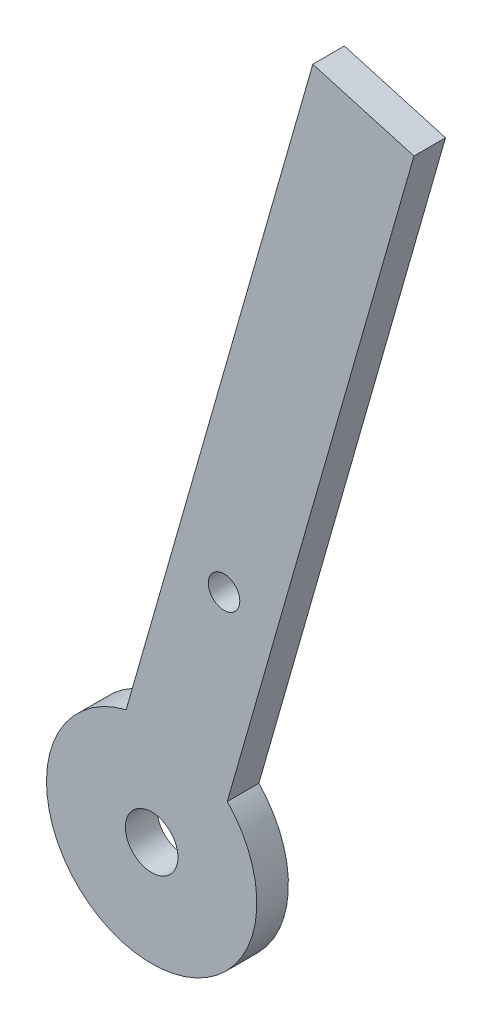
SolidWorks part; units mm, degrees
ref_plane "Front Plane" through (0, 0, 0) normal (0, 0, 1) x (1, 0, 0)
ref_plane "Top Plane" through (0, 0, 0) normal (0, 1, 0) x (1, 0, 0)
ref_plane "Right Plane" through (0, 0, 0) normal (1, 0, 0) x (0, 0, -1)
sketch "Sketch1" plane through (0, 0, 0) normal (0, 0, 1) x (1, 0, 0)
  line L2 (-60, 60) -> (128.1618, 60) construction
  line L4 (-60, -60) -> (111.0248, -60) construction
  line L8 (-60, 60) -> (-60, -60) construction
  line L10 (-87.0843, -3.037) -> (-104.8279, -65.0493)
  line L11 (-87.0843, -3.037) -> (-96.6985, -0.2861)
  line L12 (-96.6985, -0.2861) -> (-114.4421, -62.2984)
  line L13 (-112.0173, -72) -> (-91.8914, -1.6615) construction
  line L15 (-60, -60) -> (-125, -60) construction
  line L16 (-60, 60) -> (-125, 60) construction
  circle A7 centre (0, 0) radius 60 construction
  circle A9 centre (-125, 0) radius 60 construction
  arc A10 (-114.4421, -62.2984) -> (-104.8279, -65.0493) centre (-112.0173, -72) ccw
  circle A11 centre (-112.0173, -72) radius 2.5
  circle A12 centre (-105.1401, -47.9645) radius 1.5
  circle A14 centre (-112.0173, -72) radius 73.1611 construction
  point P16 (-40.3908, -55.5605)
  point P17 (-159.7602, -14.5505)
  point P18 (-158.6202, -13.8776)
  point P22 (-157.3137, -42.5709)
  point P23 (0, 0)
  point P24 (0, 0)
  point P25 (-173.2483, -30.1199)
  point P27 (-112.66, -73.4709)
  point P28 (-167.6769, -23.2375)
  point P29 (0, 0)
  point P31 (-112.6931, -73.5464)
  point P32 (0, 0)
  point P33 (0, 0)
  point P34 (0, 0)
  point P35 (0, 0)
  point P36 (-112.6931, -73.5464)
  point P37 (0, 0)
  point P38 (-87.1424, -3.1975)
  point P39 (0, 0)
  dimension "D1" = 120
  dimension "D2" = 120
  dimension "D3" = 20
  dimension "D4" = 5
  dimension "D5" = 5
  dimension "D6" = 5
  dimension "D10" = 72
  dimension "D8" = 25
  dimension "D9" = 3
  dimension "D7" = 125
extrude "Boss-Extrude1" add sketch "Sketch1" along normal blind 3
